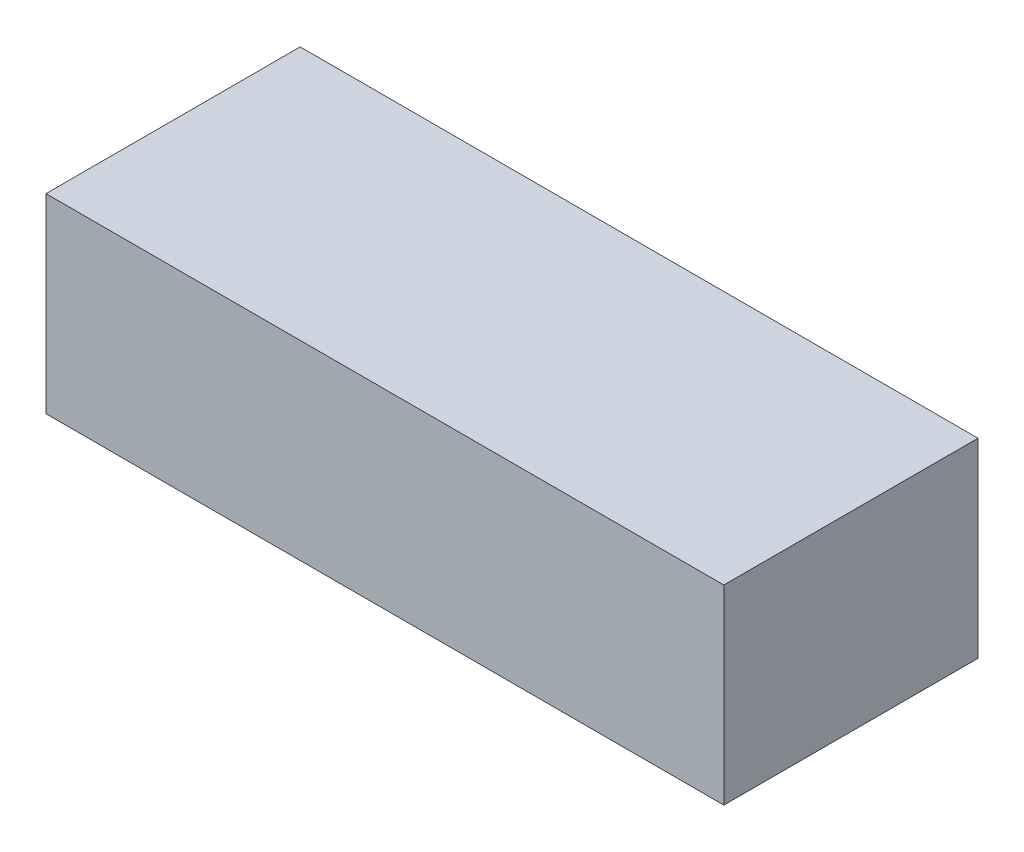
SolidWorks part; units mm, degrees
ref_plane "Front" through (0, 0, 0) normal (0, 0, 1) x (1, 0, 0)
ref_plane "Top" through (0, 0, 0) normal (0, 1, 0) x (1, 0, 0)
ref_plane "Right" through (0, 0, 0) normal (1, 0, 0) x (0, 0, -1)
sketch "草图1" plane through (0, 0, 0) normal (0, 1, 0) x (1, 0, 0)
  line L0 (0, 0) -> (160, 0)
  line L1 (160, 0) -> (160, -60)
  line L2 (160, -60) -> (0, -60)
  line L3 (0, -60) -> (0, 0)
extrude "凸台-拉伸1" add sketch "草图1" along normal blind 45
